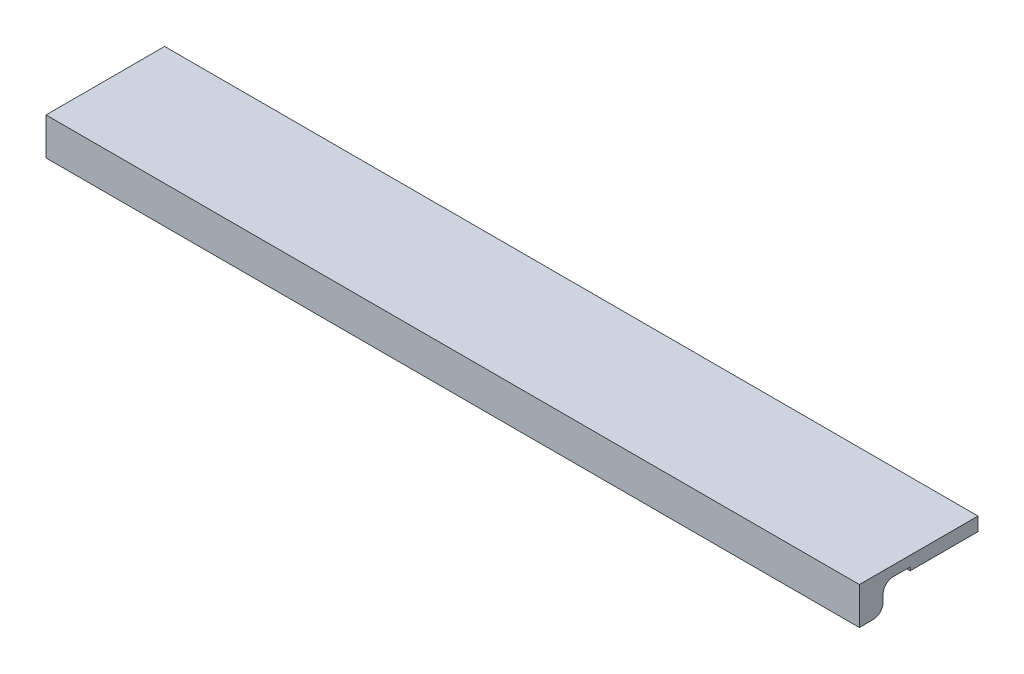
SolidWorks part; units mm, degrees
ref_plane "Front Plane" through (0, 0, 0) normal (0, 0, 1) x (1, 0, 0)
ref_plane "Top Plane" through (0, 0, 0) normal (0, 1, 0) x (1, 0, 0)
ref_plane "Right Plane" through (0, 0, 0) normal (1, 0, 0) x (0, 0, -1)
sketch "Sketch1" plane through (0, 0, 0) normal (0, 1, 0) x (1, 0, 0)
  line L1 (-120, 17.5) -> (120, 17.5)
  line L2 (-120, 17.5) -> (-120, -17.5)
  line L3 (-120, -17.5) -> (120, -17.5)
  line L4 (120, 17.5) -> (120, -17.5)
  line L5 (0, -17.5) -> (0, 17.5) construction
  line L6 (-120, 0) -> (120, 0) construction
  point P0 (0, 0)
  dimension "D1" = 35
  dimension "D2" = 240
extrude "Boss-Extrude1" add sketch "Sketch1" along normal blind 3
sketch "Sketch3" plane through (0, 0, 0) normal (0, -1, 0) x (1, 0, 0)
  line L0 (-120, -17.5) -> (-120, 17.5) construction
  line L1 (120, 17.5) -> (-120, 17.5)
  line L2 (120, 17.5) -> (120, 10.5)
  line L3 (120, 10.5) -> (-120, 10.5)
  line L4 (-120, 17.5) -> (-120, 10.5)
  line L5 (0, 10.5) -> (0, 17.5) construction
  line L6 (120, 14) -> (-120, 14) construction
  point P452 (0, 14)
  dimension "D1" = 7
extrude "Boss-Extrude3" add sketch "Sketch3" along normal blind 8
fillet "Fillet1" radius 3 2 edges at (0, 0, 10.5) (0, -8, 10.5)
sketch "Sketch4" plane through (0, 0, -17.5) normal (0, 0, -1) x (-1, 0, 0)
  line L0 (-120, -7) -> (-120, 0)
  line L1 (-120, -7) -> (120, -7)
  line L2 (-120, 0) -> (120, 0)
  line L3 (120, -7) -> (120, 0)
  line L4 (-120, -7) -> (120, 0) construction
  line L5 (-120, 0) -> (120, -7) construction
  line L6 (-120, 0) -> (120, 0) construction
  point P1 (0, -3.5)
  dimension "D1" = 7
  dimension "D2" = 240
extrude "Boss-Extrude5" add sketch "Sketch4" against normal blind 20
chamfer "Chamfer1" distance 10 distance2 6 3 edges at (-120, -7, -7.5) (0, -7, 2.5) (120, -7, -7.5)
